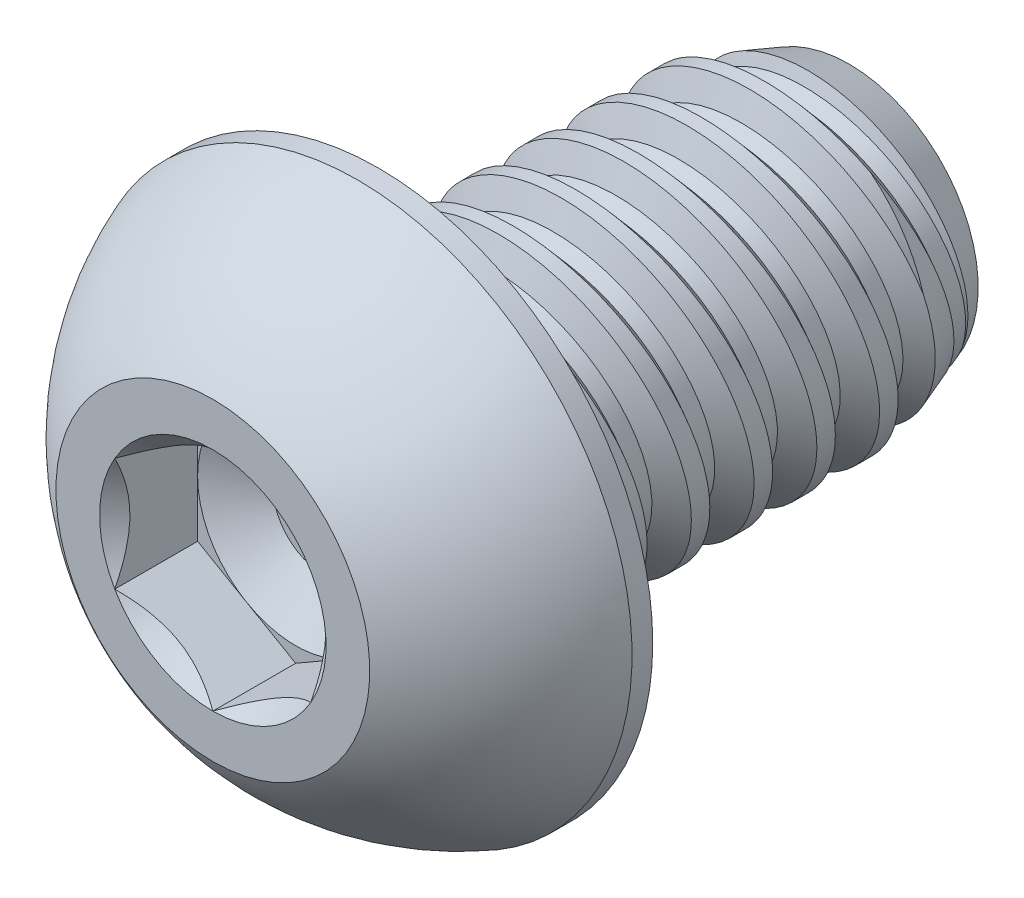
SolidWorks part; units mm, degrees
ref_plane "Front" through (0, 0, 0) normal (0, 0, 1) x (1, 0, 0)
ref_plane "Top" through (0, 0, 0) normal (0, 1, 0) x (1, 0, 0)
ref_plane "Right" through (0, 0, 0) normal (1, 0, 0) x (0, 0, -1)
sketch "Sketch1" plane through (0, 0, 0) normal (1, 0, 0) x (0, 0, -1)
  line L0 (0, 0) -> (-3.3528, 0) construction
  line L1 (0, 0) -> (9.525, 0)
  line L2 (0, 0) -> (0, 3.175)
  line L3 (0, 3.175) -> (9.525, 3.175)
  line L4 (9.525, 0) -> (9.525, 3.175)
  line L5 (0, -3.175) -> (9.525, -3.175) construction
  dimension "D1" = 9.525
  dimension "Thread Dia" = 6.35
  dimension "Length" = 9.525
  dimension "Head Height" = 3.3528
revolve "Revolve1" add sketch "Sketch1" angle 360 about L0
ref_plane "Plane1" through (0, 0, 3.3528) normal (0, 0, 1) x (1, 0, 0)
sketch "Sketch2" plane through (0, 0, 0) normal (1, 0, 0) x (0, 0, -1)
  line L0 (0, 3.175) -> (0, -3.175) construction
  line L1 (0, -3.175) -> (1.27, -3.175) construction
  line L2 (1.27, -3.175) -> (0, 3.175) construction
  line L3 (0, 3.175) -> (0.1557, 3.2061) construction
  line L4 (0.1557, 3.2061) -> (1.2453, 3.4241)
  line L5 (1.2453, 3.4241) -> (0.991, 2.6722)
  line L6 (0.991, 2.6722) -> (0.6796, 2.6099)
  line L7 (0.6796, 2.6099) -> (0.1557, 3.2061)
  line L8 (0.8353, 2.641) -> (0.7005, 3.3151) construction
  line L9 (0, -3.175) -> (9.525, -3.175) construction
  line L10 (0, 3.175) -> (9.525, 3.175) construction
  line L12 (0.7285, 3.175) -> (1.9985, -3.175) construction
  line L13 (0, -0.2727) -> (2.727, 0.2727) construction
  line L15 (0, 0) -> (0, 3.175) construction
  point P19 (1.3635, 0)
  dimension "D1" = 60
  dimension "Thread Pitch" = 1.27
  dimension "D2" = 0.1588
  dimension "D3" = 0.3175
  dimension "D4" = 1.27
revolve "Cut-Revolve1" cut sketch "Sketch2" angle 360 about L13
sketch "Sketch3" plane through (0, 0, 0) normal (1, 0, 0) x (0, 0, -1)
  line L0 (9.525, 2.6099) -> (7.9724, 3.175)
  line L1 (7.9724, 3.175) -> (9.525, 3.175)
  line L2 (9.525, 3.175) -> (9.525, 2.6099)
  line L3 (0, 3.175) -> (9.525, 3.175) construction
  line L4 (9.525, 0) -> (9.525, 3.175) construction
  line L5 (7.9724, 0) -> (0, 0) construction
  line L6 (7.9724, 3.175) -> (7.9724, -3.175) construction
  line L7 (0, -3.175) -> (9.525, -3.175) construction
  dimension "D1" = 20
  dimension "D2" = 6.35
revolve "Cut-Revolve2" cut sketch "Sketch3" angle 360 about L5
pattern_linear "LPattern1" count 7 spacing 1.27 along (0, 0, 1)
pattern_linear "LPattern2" count 2 spacing 1.27 along (0, 0, 1)
sketch "Sketch4" plane through (0, 0, 0) normal (0, 0, 1) x (1, 0, 0)
  circle A0 centre (0, 0) radius 5.5499
  dimension "Head Dia" = 11.0998
extrude "Extrude1" add sketch "Sketch4" along normal up to surface (3.3528 mm away)
sketch "Sketch9" plane through (0, 0, 0) normal (1, 0, 0) x (0, 0, -1)
  line L0 (0, 5.5499) -> (-0.4191, 5.5499)
  line L1 (0, 5.5499) -> (0, 5.969)
  line L2 (0, 5.969) -> (-3.7719, 5.969)
  line L3 (0, 0) -> (-3.3528, 0) construction
  line L4 (-3.7719, 5.969) -> (-3.7719, 3.175)
  line L5 (-3.7719, 3.175) -> (-3.3528, 3.175)
  line L6 (0, 0) -> (0, 3.175) construction
  line L10 (0, 5.5499) -> (-3.3528, 5.5499) construction
  line L11 (0, 3.175) -> (9.525, 3.175) construction
  line L12 (-3.3528, 5.5499) -> (-3.3528, -5.5499) construction
  arc A0 (-3.3528, 3.175) -> (-0.4191, 5.5499) centre (1.6456, 0) cw
  dimension "Side Head Height" = 0.4191
revolve "Cut-Revolve3" cut sketch "Sketch9" angle 360 about L3
sketch "Sketch6" plane through (0, 0, 3.3528) normal (0, 0, 1) x (1, 0, 0)
  line L1 (0, -2.2914) -> (1.9844, -1.1457)
  line L2 (1.9844, -1.1457) -> (1.9844, 1.1457)
  line L3 (1.9844, 1.1457) -> (0, 2.2914)
  line L4 (0, 2.2914) -> (-1.9844, 1.1457)
  line L5 (-1.9844, 1.1457) -> (-1.9844, -1.1457)
  line L6 (-1.9844, -1.1457) -> (0, -2.2914)
  circle A0 centre (0, 0) radius 1.9844 construction
  dimension "Hex" = 3.9688
extrude "Cut-Extrude1" cut sketch "Sketch6" against normal blind 1.6764
sketch "Sketch7" plane through (0, 0, 3.3528) normal (0, 0, 1) x (1, 0, 0)
  circle A0 centre (0, 0) radius 2.2914
extrude "Cut-Extrude4" cut sketch "Sketch7" against normal blind 1.6764 draft 45
sketch "Sketch8" plane through (0, 0, 1.6764) normal (0, 0, 1) x (1, 0, 0)
  circle A0 centre (0, 0) radius 1.9844 construction
  circle A1 centre (0, 0) radius 1.9844
extrude "Cut-Extrude5" cut sketch "Sketch8" against normal blind 0.5588 draft 60
equation "\"D2@Sketch2\"=\"Thread Pitch@Sketch2\"/8"
equation "\"D3@Sketch2\"=\"Thread Pitch@Sketch2\"/4"
equation "\"D4@Sketch2\"=\"Thread Pitch@Sketch2\""
equation "\"D3@LPattern1\"=\"Thread Pitch@Sketch2\""
equation "\"D1@Cut-Extrude1\"=\"Head Height@Sketch1\"/2"
equation "\"D1@Cut-Extrude4\"=\"D1@Cut-Extrude1\""
equation "\"D1@Cut-Extrude5\"=\"D1@Cut-Extrude1\"/3"
equation "\"D1@LPattern1\"=\"D1@Sketch1\"/\"Thread Pitch@Sketch2\""
equation "\"D3@LPattern2\"=\"Thread Pitch@Sketch2\""
equation "\"Side Head Height@Sketch9\"=\"Head Height@Sketch1\"/8"
